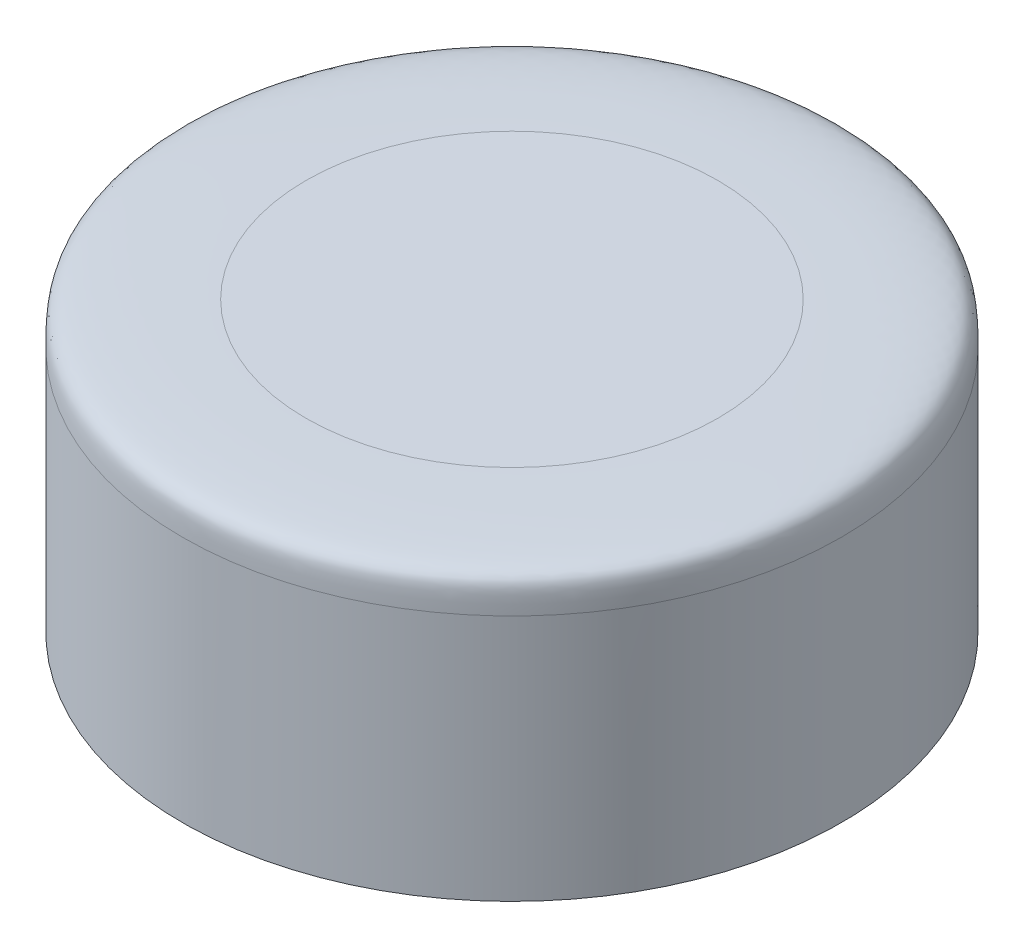
SolidWorks part; units mm, degrees
ref_plane "前视基准面" through (0, 0, 0) normal (0, 0, 1) x (1, 0, 0)
ref_plane "上视基准面" through (0, 0, 0) normal (0, 1, 0) x (1, 0, 0)
ref_plane "右视基准面" through (0, 0, 0) normal (1, 0, 0) x (0, 0, -1)
sketch "草图1" plane through (0, 0, 0) normal (0, 0, 1) x (1, 0, 0)
  line L1 (0, 8) -> (8, 8)
  line L2 (8, 8) -> (8, 1)
  line L3 (8, 1) -> (3.9, 1)
  line L6 (3.9, 1) -> (3.9, 0.4)
  line L7 (3.9, 0.4) -> (2.9, 0.4)
  line L8 (0, 8) -> (0, 5.4)
  line L9 (0, 5.4) -> (2.9, 5.4)
  line L10 (2.9, 5.4) -> (2.9, 0.4)
  point P5 (4.9, 1)
  point P8 (6, 0.6666)
  point P13 (4.9471, 1)
  dimension "D1" = 2.9
  dimension "D2" = 1
  dimension "D5" = 5.4
  dimension "D6" = 8
  dimension "D7" = 5
  dimension "D8" = 8
  dimension "D9" = 7
revolve "旋转1" add sketch "草图1" angle 360 about L8
sketch "草图2" plane through (0, 0, 0) normal (0, 0, 1) x (1, 0, 0)
  line L0 (0, 0) -> (0, -1.7025) construction
  line L1 (5, 8) -> (8, 8)
  line L2 (8, 8) -> (-8, 8) construction
  line L3 (8, 8) -> (8, 7)
  line L4 (8, 1) -> (8, 8) construction
  spline S0 degree 3 poles (5, 8) (5.6935, 8) (7.4649, 7.98) (7.9897, 7.7047) (8, 7.5154) (8, 7) knots 0 0 0 0 0.505788 0.605788 1 1 1 1
  point P12 (7.637, 7.6774)
  point P13 (0, 0)
  point P14 (0, 0)
  point P15 (7.7143, 7.7501)
  point P16 (7.7612, 7.8212)
  dimension "D1" = 3
  dimension "D2" = 1
revolve "切除-旋转1" cut sketch "草图2" angle 360 about L0
